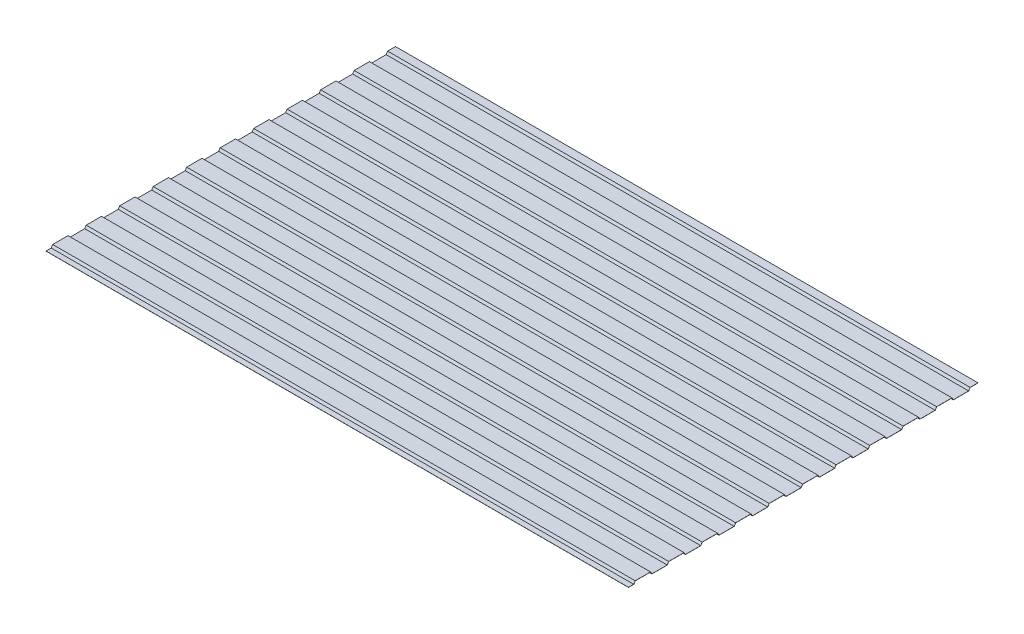
SolidWorks part; units mm, degrees
ref_plane "Спереди" through (0, 0, 0) normal (0, 0, 1) x (1, 0, 0)
ref_plane "Сверху" through (0, 0, 0) normal (0, 1, 0) x (1, 0, 0)
ref_plane "Справа" through (0, 0, 0) normal (1, 0, 0) x (0, 0, -1)
sketch "Эскиз1" plane through (0, 0, 0) normal (1, 0, 0) x (0, 0, -1)
  line L0 (0, 0) -> (5, 8)
  line L1 (5, 8) -> (57.5, 8)
  line L2 (57.5, 8) -> (62.5, 0)
  line L3 (62.5, 0) -> (115, 0)
  line L4 (115, 0) -> (120, 8)
  line L5 (120, 8) -> (172.5, 8)
  line L6 (172.5, 8) -> (177.5, 0)
  line L7 (177.5, 0) -> (230, 0)
  line L8 (230, 0) -> (235, 8)
  line L9 (235, 8) -> (287.5, 8)
  line L10 (287.5, 8) -> (292.5, 0)
  line L11 (292.5, 0) -> (345, 0)
  line L12 (345, 0) -> (350, 8)
  line L13 (350, 8) -> (402.5, 8)
  line L14 (402.5, 8) -> (407.5, 0)
  line L15 (407.5, 0) -> (460, 0)
  line L16 (460, 0) -> (465, 8)
  line L17 (465, 8) -> (517.5, 8)
  line L18 (517.5, 8) -> (522.5, 0)
  line L19 (522.5, 0) -> (575, 0)
  line L20 (575, 0) -> (580, 8)
  line L21 (580, 8) -> (632.5, 8)
  line L22 (632.5, 8) -> (637.5, 0)
  line L23 (637.5, 0) -> (690, 0)
  line L24 (690, 0) -> (695, 8)
  line L25 (695, 8) -> (747.5, 8)
  line L26 (747.5, 8) -> (752.5, 0)
  line L27 (752.5, 0) -> (805, 0)
  line L28 (805, 0) -> (810, 8)
  line L29 (810, 8) -> (862.5, 8)
  line L30 (862.5, 8) -> (867.5, 0)
  line L31 (867.5, 0) -> (920, 0)
  line L32 (920, 0) -> (925, 8)
  line L33 (925, 8) -> (977.5, 8)
  line L34 (977.5, 8) -> (982.5, 0)
  line L35 (982.5, 0) -> (1035, 0)
  line L36 (1035, 0) -> (1040, 8)
  line L37 (1040, 8) -> (1092.5, 8)
  line L38 (1092.5, 8) -> (1097.5, 0)
  line L39 (1097.5, 0) -> (1150, 0)
  line L40 (0, 0) -> (-18, 0)
  line L41 (1150, 0) -> (1155, 8)
  line L42 (1155, 8) -> (1182, 8)
  dimension "D1" = 8
  dimension "D2" = 62.5
  dimension "D3" = 52.5
  dimension "D4" = 5
  dimension "D5" = 52.5
  dimension "D7" = 5
  dimension "D9" = 18
  dimension "D10" = 1200
  dimension "D6" = 10
extrude "Вытянуть-Тонкостенный1" add sketch "Эскиз1" along normal blind 2000 thin thin type mid plane wall 0.4
